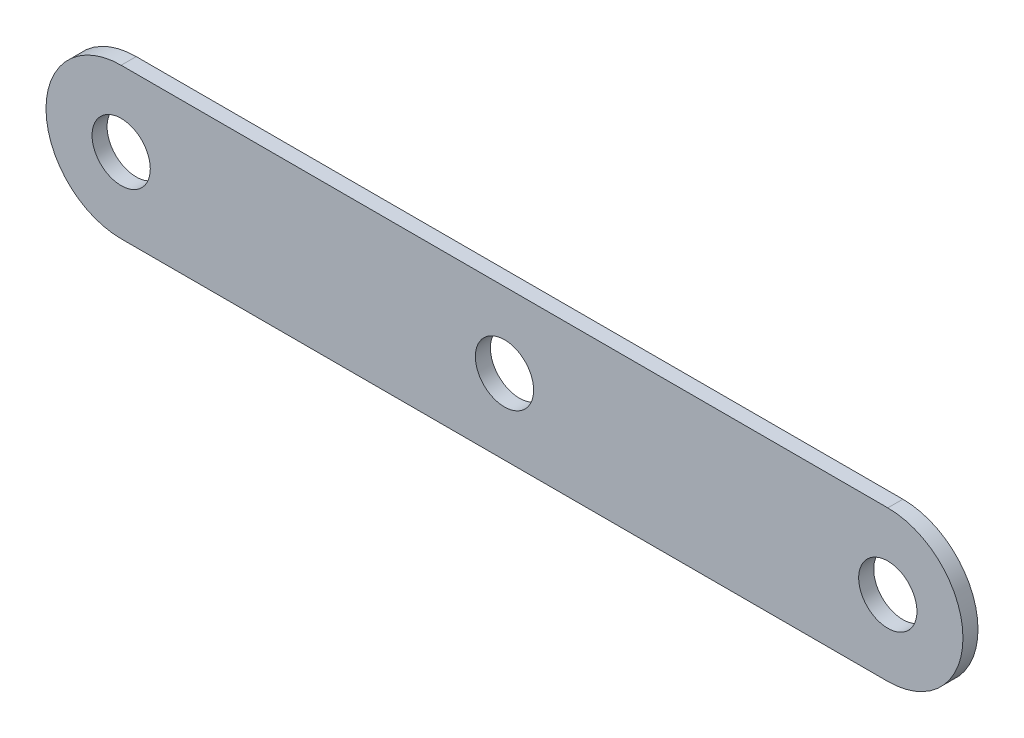
SolidWorks part; units mm, degrees
ref_plane "Front Plane" through (0, 0, 0) normal (0, 0, 1) x (1, 0, 0)
ref_plane "Top Plane" through (0, 0, 0) normal (0, 1, 0) x (1, 0, 0)
ref_plane "Right Plane" through (0, 0, 0) normal (1, 0, 0) x (0, 0, -1)
sketch "Sketch1" plane through (0, 0, 0) normal (0, 0, 1) x (1, 0, 0)
  line L0 (0, 0) -> (204, 0) construction
  line L1 (0, 20) -> (204, 20)
  line L2 (0, -20) -> (204, -20)
  arc A0 (0, 20) -> (0, -20) centre (0, 0) ccw
  arc A1 (204, -20) -> (204, 20) centre (204, 0) ccw
  point P3 (102, 0)
  dimension "D2" = 20
  dimension "D1" = 204
extrude "Boss-Extrude1" add sketch "Sketch1" along normal blind 4
sketch "Sketch2" plane through (0, 0, 4) normal (0, 0, 1) x (1, 0, 0)
  circle A0 centre (0, 0) radius 7.75
  circle A1 centre (204, 0) radius 7.75
  arc A2 (204, -20) -> (204, 20) centre (204, 0) ccw construction
  dimension "D1" = 0
  dimension "D2" = 15.5
  dimension "D3" = 15.5
extrude "Cut-Extrude1" cut sketch "Sketch2" against normal up to next
sketch "Sketch3" plane through (0, 0, 4) normal (0, 0, 1) x (1, 0, 0)
  circle A0 centre (102, 0) radius 7.75
  dimension "D1" = 102
  dimension "D2" = 15.5
extrude "Cut-Extrude2" cut sketch "Sketch3" against normal up to next
